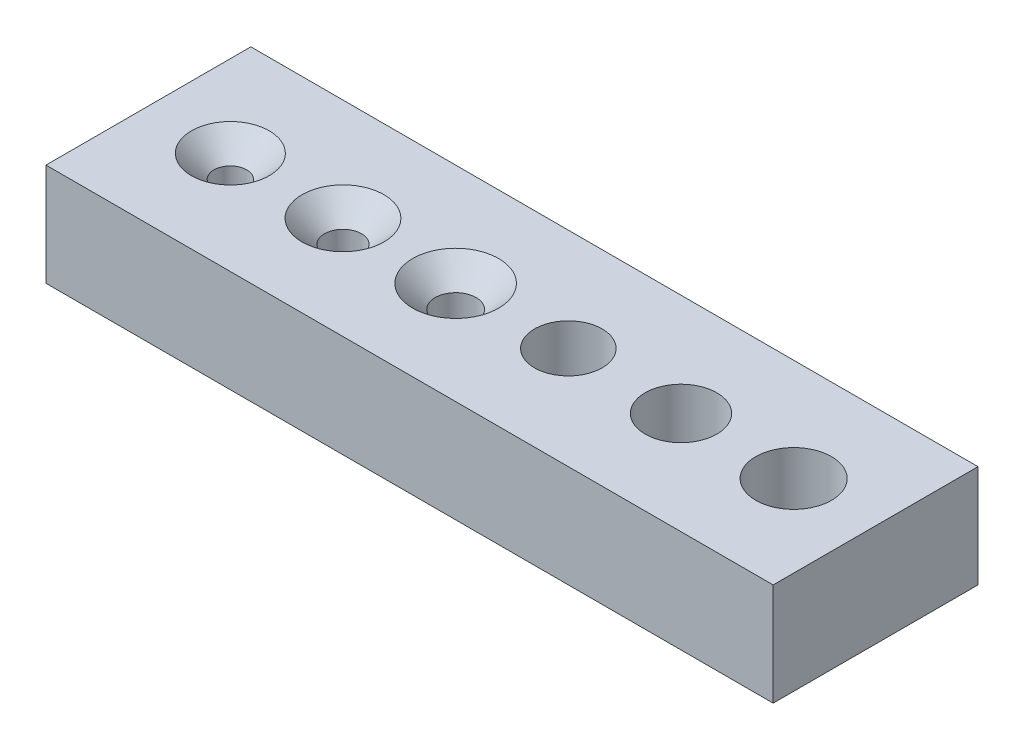
SolidWorks part; units mm, degrees
other "Markup1"
sketch "Sketch9" plane through (35.5, 5, 0) normal (0.0752, 0.9276, 0.366) x (0.9954, -0.0476, -0.0837)
ref_plane "Front Plane" through (0, 0, 0) normal (0, 0, 1) x (1, 0, 0)
ref_plane "Top Plane" through (0, 0, 0) normal (0, 1, 0) x (1, 0, 0)
ref_plane "Right Plane" through (0, 0, 0) normal (1, 0, 0) x (0, 0, -1)
sketch "Sketch1" plane through (0, 0, 0) normal (0, 1, 0) x (1, 0, 0)
  line L1 (0, 0) -> (35.5, 0)
  line L2 (0, 0) -> (0, 10)
  line L3 (0, 10) -> (35.5, 10)
  line L4 (35.5, 0) -> (35.5, 10)
  dimension "D1" = 10
  dimension "D2" = 35.5
extrude "Boss-Extrude1" add sketch "Sketch1" along normal blind 5
sketch "Sketch2" plane through (0, 5, 0) normal (0, 1, 0) x (1, 0, 0)
  line L0 (0, 10) -> (0, 0) construction
  line L1 (0, 0) -> (35.5, 0) construction
  point P0 (4, 5)
  point P5 (9.5, 5)
  point P6 (31.5, 5)
  point P7 (15, 5)
  point P8 (20.5, 5)
  point P9 (26, 5)
  dimension "D1" = 4
  dimension "D2" = 5
  dimension "D3" = 5
  dimension "D4" = 2
hole_wizard "Tap Drill for M2x0.4 Tap1" positions "3DSketch1" profile "Sketch3" hole size "M2x0.4" standard "ANSI Metric"
sketch3d "3DSketch1"
  point P11 (9.5, 5, -5)
sketch "Sketch3" plane through (9.5, 5, -5) normal (1, 0, 0) x (0, 0, 1)
  line L0 (0, 0) -> (0, 7.5408)
  line L1 (0, 7.5408) -> (0.9, 7)
  line L2 (0.9, 7) -> (0.9, 1.1)
  line L3 (0.9, 1.1) -> (2, 0)
  line L5 (2, 0) -> (0, 0)
  line L6 (-0.9, 1.1) -> (-2, 0) construction
  line L10 (0, 7.5408) -> (-0.9, 7) construction
  line L11 (0, -6.35) -> (0, 107.95) construction
  dimension "Hole Dia." = 1.8
  dimension "Hole Depth" = 7
  dimension "Near C'Sink Dia." = 4
  dimension "Near C'Sink Angle" = 90
  dimension "Drill Angle" = 118
hole_wizard "Tap Drill for M2x0.4 Tap2" positions "3DSketch2" profile "Sketch4" hole size "M2x0.4" standard "ANSI Metric"
sketch3d "3DSketch2"
  point P4 (15, 5, -5)
sketch "Sketch4" plane through (15, 5, -5) normal (1, 0, 0) x (0, 0, 1)
  line L0 (0, 0) -> (0, 7.6009)
  line L1 (0, 7.6009) -> (1, 7)
  line L2 (1, 7) -> (1, 1.1)
  line L3 (1, 1.1) -> (2.1, 0)
  line L5 (2.1, 0) -> (0, 0)
  line L6 (-1, 1.1) -> (-2.1, 0) construction
  line L10 (0, 7.6009) -> (-1, 7) construction
  line L11 (0, -6.35) -> (0, 107.95) construction
  dimension "Hole Dia." = 2
  dimension "Hole Depth" = 7
  dimension "Near C'Sink Dia." = 4.2
  dimension "Near C'Sink Angle" = 90
  dimension "Drill Angle" = 118
hole_wizard "Tap Drill for M2x0.4 Tap3" positions "3DSketch3" profile "Sketch5" hole size "M2x0.4" standard "ANSI Metric"
sketch3d "3DSketch3"
  point P0 (4, 5, -5)
sketch "Sketch5" plane through (4, 5, -5) normal (1, 0, 0) x (0, 0, 1)
  line L0 (0, 0) -> (0, 7.4807)
  line L1 (0, 7.4807) -> (0.8, 7)
  line L2 (0.8, 7) -> (0.8, 1.1)
  line L3 (0.8, 1.1) -> (1.9, 0)
  line L5 (1.9, 0) -> (0, 0)
  line L6 (-0.8, 1.1) -> (-1.9, 0) construction
  line L10 (0, 7.4807) -> (-0.8, 7) construction
  line L11 (0, -6.35) -> (0, 107.95) construction
  dimension "Hole Dia." = 1.6
  dimension "Hole Depth" = 7
  dimension "Near C'Sink Dia." = 3.8
  dimension "Near C'Sink Angle" = 90
  dimension "Drill Angle" = 118
hole_wizard "Tap Drill for M4x0.7 Tap1" positions "3DSketch4" profile "Sketch6" hole size "M4x0.7" standard "ANSI Metric"
sketch3d "3DSketch4"
  point P0 (20.5, 5, -5)
sketch "Sketch6" plane through (20.5, 5, -5) normal (1, 0, 0) x (0, 0, 1)
  line L0 (0, 0) -> (0, 5.9914)
  line L1 (0, 5.9914) -> (1.65, 5)
  line L2 (1.65, 5) -> (1.65, 0)
  line L5 (1.65, 0) -> (0, 0)
  line L10 (0, 5.9914) -> (-1.65, 5) construction
  line L11 (0, -6.35) -> (0, 107.95) construction
  dimension "Hole Dia." = 3.3
  dimension "Hole Depth" = 5
  dimension "Drill Angle" = 118
hole_wizard "Tap Drill for M4x0.7 Tap2" positions "3DSketch5" profile "Sketch7" hole size "M4x0.7" standard "ANSI Metric"
sketch3d "3DSketch5"
  point P0 (26, 5, -5)
sketch "Sketch7" plane through (26, 5, -5) normal (1, 0, 0) x (0, 0, 1)
  line L0 (0, 0) -> (0, 6.0515)
  line L1 (0, 6.0515) -> (1.75, 5)
  line L2 (1.75, 5) -> (1.75, 0)
  line L5 (1.75, 0) -> (0, 0)
  line L10 (0, 6.0515) -> (-1.75, 5) construction
  line L11 (0, -6.35) -> (0, 107.95) construction
  dimension "Hole Dia." = 3.5
  dimension "Hole Depth" = 5
  dimension "Drill Angle" = 118
hole_wizard "Tap Drill for M4x0.7 Tap3" positions "3DSketch6" profile "Sketch8" hole size "M4x0.7" standard "ANSI Metric"
sketch3d "3DSketch6"
  point P0 (31.5, 5, -5)
sketch "Sketch8" plane through (31.5, 5, -5) normal (1, 0, 0) x (0, 0, 1)
  line L0 (0, 0) -> (0, 6.1116)
  line L1 (0, 6.1116) -> (1.85, 5)
  line L2 (1.85, 5) -> (1.85, 0)
  line L5 (1.85, 0) -> (0, 0)
  line L10 (0, 6.1116) -> (-1.85, 5) construction
  line L11 (0, -6.35) -> (0, 107.95) construction
  dimension "Hole Dia." = 3.7
  dimension "Hole Depth" = 5
  dimension "Drill Angle" = 118
